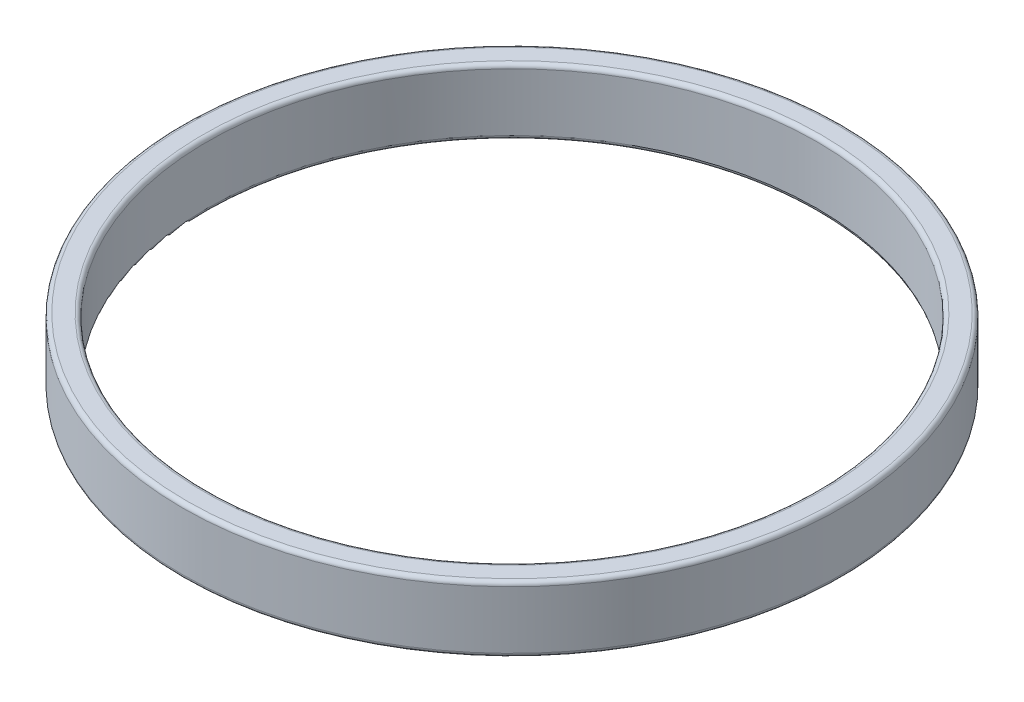
SolidWorks part; units mm, degrees
material "Rubber"
ref_plane "Front Plane" through (0, 0, 0) normal (0, 0, 1) x (1, 0, 0)
ref_plane "Top Plane" through (0, 0, 0) normal (0, 1, 0) x (1, 0, 0)
ref_plane "Right Plane" through (0, 0, 0) normal (1, 0, 0) x (0, 0, -1)
sketch "Sketch1" plane through (0, 0, 0) normal (0, 0, 1) x (1, 0, 0)
  line L0 (0, 0) -> (0, 18.1977) construction
  line L1 (-18.5, 0) -> (0, 0) construction
  line L2 (-20, 2) -> (-18.5, 2)
  line L3 (-20, 2) -> (-20, -2)
  line L4 (-20, -2) -> (-18.5, -2)
  line L5 (-18.5, 2) -> (-18.5, -2)
  dimension "D1" = 1.5
  dimension "D2" = 4
  dimension "D3" = 20
revolve "Revolve1" add sketch "Sketch1" angle 360 about L0
fillet "Fillet1" radius 0.25 4 edges at (0, -2, -18.5) (0, -2, -20) (0, 2, -20) (0, 2, -18.5)
